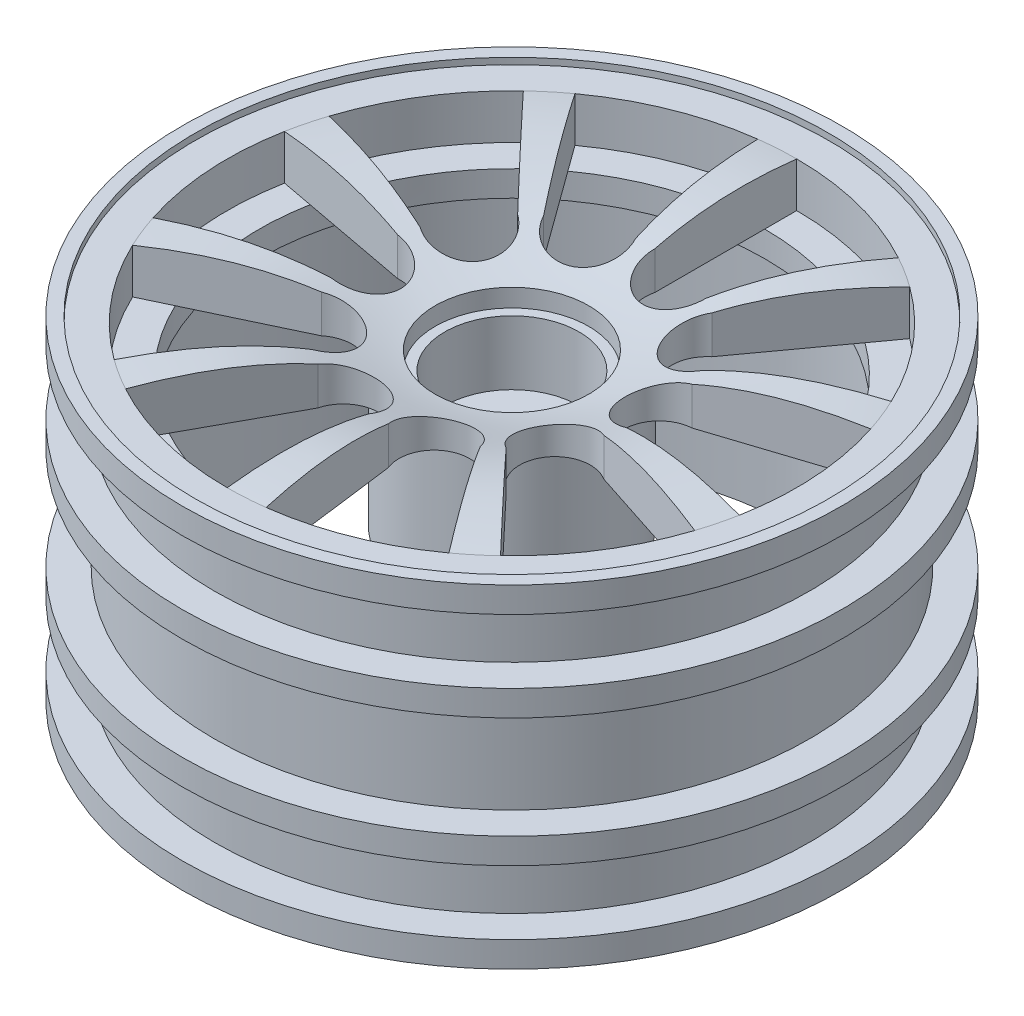
SolidWorks part; units mm, degrees
ref_plane "Front Plane" through (0, 0, 0) normal (0, 0, 1) x (1, 0, 0)
ref_plane "Top Plane" through (0, 0, 0) normal (0, 1, 0) x (1, 0, 0)
ref_plane "Right Plane" through (0, 0, 0) normal (1, 0, 0) x (0, 0, -1)
sketch "Sketch2" plane through (0, 0, 0) normal (0, 0, 1) x (1, 0, 0)
  line L0 (0, 0) -> (25.75, 0)
  line L1 (0, 14.3302) -> (0, -14.3302) construction
  line L2 (22.25, -5.5) -> (22.25, -25.5)
  line L3 (25.75, 0) -> (24.75, 0)
  line L4 (25.75, 0) -> (25.75, -2)
  line L5 (25.75, -26) -> (24.75, -26)
  line L6 (24.75, 0) -> (24.75, -0.5)
  line L7 (24.75, -0.5) -> (22.25, -0.5)
  line L9 (24.75, -25.5) -> (22.25, -25.5)
  line L11 (22.25, -4) -> (18.9196, -4)
  line L13 (22.25, -5.5) -> (18.9196, -5.5)
  line L14 (18.9196, -4) -> (18.9196, -5.5)
  line L15 (24.75, -25.5) -> (24.75, -26)
  line L16 (25.75, -24) -> (25.75, -26)
  line L17 (25.75, -2) -> (23.25, -2)
  line L19 (25.75, -24) -> (23.25, -24)
  line L20 (23.25, -2) -> (23.25, -5.5)
  line L21 (23.25, -9) -> (23.25, -17)
  line L26 (23.25, -17) -> (25.75, -17)
  line L28 (23.25, -19) -> (25.75, -19)
  line L29 (25.75, -17) -> (25.75, -19)
  line L30 (23.25, -7) -> (23.25, -5.5)
  line L31 (23.25, -19) -> (23.25, -24)
  line L32 (23.25, -7) -> (25.75, -7)
  line L34 (23.25, -9) -> (25.75, -9)
  line L35 (25.75, -7) -> (25.75, -9)
  line L36 (6, -9.2028) -> (6, -14.3028)
  line L37 (22.25, -4) -> (7.93, -4)
  line L41 (6, -3.7028) -> (4.5, -3.7028)
  line L43 (6, -9.2028) -> (4.5, -9.2028)
  line L44 (22.25, -4) -> (22.25, -5.5)
  line L45 (4.5, -3.7028) -> (4.5, -9.2028)
  line L47 (7.93, -4) -> (7.93, -14.3028)
  line L48 (7.93, -14.3028) -> (6, -14.3028)
  line L49 (6, -2.3028) -> (6, -3.7028)
  spline S0 degree 3 poles (22.25, -0.5) (18.957, -0.1122) (13.3391, -0.0971) (8.1282, -1.9463) (6, -2.3028) knots 0 0 0 0 0.607536 1 1 1 1
  dimension "D17" = 6
  dimension "D1" = 25.75
  dimension "D2" = 1
  dimension "D3" = 26
  dimension "D4" = 2.5
  dimension "D5" = 25
  dimension "D6" = 20
  dimension "D7" = 4
  dimension "D8" = 2
  dimension "D9" = 2
  dimension "D10" = 2.5
  dimension "D11" = 2
  dimension "D12" = 2
  dimension "D13" = 5
  dimension "D14" = 5
  dimension "D15" = 14.32
  dimension "D16" = 1.4
  dimension "D18" = 12
  dimension "D19" = 1.5
  dimension "D20" = 5.5
revolve "Revolve1" add sketch "Sketch2" angle 360 about L1
sketch "Sketch4" plane through (0, -3.7028, 0) normal (0, 1, 0) x (1, 0, 0)
  circle A0 centre (0, 0) radius 4.5
extrude "Boss-Extrude1" add sketch "Sketch4" against normal up to surface (5.5 mm away) up to face at (0, -9.2028, 4.5)
sketch "Sketch5" plane through (0, -14.3028, 0) normal (0, -1, 0) x (1, 0, 0)
  line L1 (1.0737, -6.8445) -> (6.4644, -2.4924)
  line L2 (6.4644, -2.4924) -> (5.3906, 4.3521)
  line L3 (5.3906, 4.3521) -> (-1.0737, 6.8445)
  line L4 (-1.0737, 6.8445) -> (-6.4644, 2.4924)
  line L5 (-6.4644, 2.4924) -> (-5.3906, -4.3521)
  line L6 (-5.3906, -4.3521) -> (1.0737, -6.8445)
  circle A0 centre (0, 0) radius 6 construction
  dimension "D1" = 12
extrude "Cut-Extrude1" cut sketch "Sketch5" against normal blind 5
sketch "Sketch6" plane through (0, -3.7028, 0) normal (0, 1, 0) x (1, 0, 0)
  circle A0 centre (0, 0) radius 5.25
  dimension "D1" = 10.5
extrude "Cut-Extrude2" cut sketch "Sketch6" against normal blind 5
sketch "Sketch7" plane through (0, -9.2028, 0) normal (0, -1, 0) x (-1, 0, 0)
  circle A0 centre (0, 0) radius 2
  dimension "D1" = 4
extrude "Cut-Extrude3" cut sketch "Sketch7" against normal through all
sketch "Sketch8" plane through (0, 0, 0) normal (0, 1, 0) x (1, 0, 0)
  line L0 (0, 22.25) -> (0, 0) construction
  line L1 (0, 0) -> (10.6586, 19.5309) construction
  line L2 (0, 22.25) -> (0, 11.1788)
  line L3 (10.6586, 19.5309) -> (5.3551, 9.8127)
  circle A1 centre (0, 0) radius 22.25 construction
  arc A2 (0, 11.1788) -> (5.3551, 9.8127) centre (2.6775, 10.4957) ccw
  arc A3 (0, 22.25) -> (10.6586, 19.5309) centre (0, 0) cw
  point P5 (0, 11.1788)
  dimension "D1" = 11
extrude "Cut-Extrude4" cut sketch "Sketch8" against normal through all
pattern_circular "CirPattern1" count 10 every 36 about axis through (0, 0, 0) along (0, 1, 0) of "Cut-Extrude4"
sketch "Sketch10" plane through (0, -4, 0) normal (0, -1, 0) x (1, 0, 0)
  circle A0 centre (0, 0) radius 22.25
  circle A1 centre (0, 0) radius 19.75
  dimension "D1" = 44.5
  dimension "D2" = 2.5
extrude "Boss-Extrude4" add sketch "Sketch10" along normal blind 2
